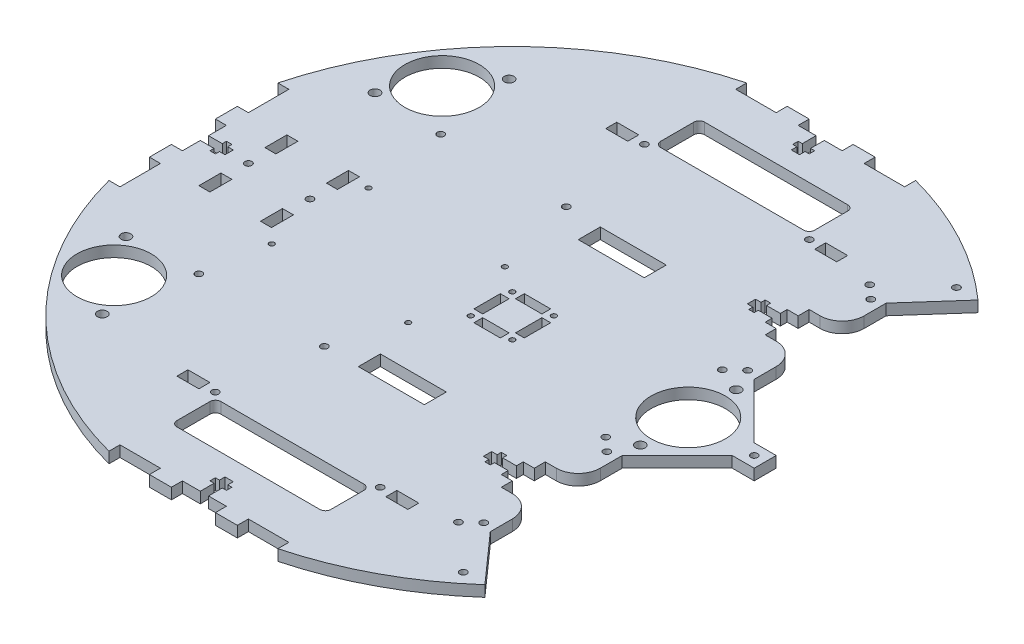
SolidWorks part; units mm, degrees
ref_plane "Front Plane" through (0, 0, 0) normal (0, 0, 1) x (1, 0, 0)
ref_plane "Top Plane" through (0, 0, 0) normal (0, 1, 0) x (1, 0, 0)
ref_plane "Right Plane" through (0, 0, 0) normal (1, 0, 0) x (0, 0, -1)
sketch "Sketch1" plane through (0, 0, 0) normal (0, 1, 0) x (1, 0, 0)
  line L0 (0, 0) -> (0, 177.8)
  line L1 (0, 0) -> (127, 0)
  line L2 (76.2, 82.55) -> (76.2, 69.85)
  line L3 (25.4, 0) -> (25.4, 38.1)
  line L4 (25.4, 38.1) -> (25.4, 114.3)
  line L6 (82.55, -88.9) -> (88.9, -88.9)
  line L7 (101.6, -38.1) -> (127, -12.7)
  line L8 (19.05, -184.15) -> (25.4, -184.15)
  line L9 (101.6, -101.6) -> (101.6, -114.3)
  line L12 (-19.05, -184.15) -> (-25.4, -184.15)
  line L13 (76.2, -82.55) -> (76.2, -69.85)
  line L14 (82.55, 63.5) -> (88.9, 63.5)
  line L15 (101.6, 38.1) -> (101.6, 50.8)
  line L16 (82.55, -63.5) -> (82.55, -69.85)
  line L17 (101.6, -38.1) -> (101.6, -50.8)
  line L18 (88.9, -63.5) -> (82.55, -63.5)
  line L19 (-25.4, -177.8) -> (-25.4, -184.15)
  line L20 (-177.8, -25.4) -> (-184.15, -25.4)
  line L21 (101.6, 38.1) -> (127, 12.7)
  line L22 (82.55, 88.9) -> (88.9, 88.9)
  line L23 (133.35, -6.35) -> (146.05, -6.35)
  line L24 (101.6, 114.3) -> (126.5613, 142.3815)
  line L25 (101.6, -114.3) -> (126.5613, -142.3815)
  line L26 (101.6, 101.6) -> (101.6, 114.3)
  line L27 (0, 0) -> (-177.8, 0)
  line L28 (133.35, 6.35) -> (146.05, 6.35)
  line L29 (146.05, -6.35) -> (146.05, 6.35)
  line L30 (-177.8, 0) -> (-177.8, 6.35)
  line L31 (-177.8, 0) -> (-177.8, -6.35)
  line L32 (-184.15, 48.7753) -> (-177.8, 48.7753)
  line L33 (-19.05, 184.15) -> (-25.4, 184.15)
  line L34 (0, 177.8) -> (6.35, 177.8)
  line L35 (-25.4, 177.8) -> (-25.4, 184.15)
  line L36 (-184.15, 19.05) -> (-184.15, 12.7)
  line L37 (82.55, -69.85) -> (76.2, -69.85)
  line L38 (-177.8, 48.7753) -> (-177.8, 25.4)
  line L39 (76.2, 82.55) -> (82.55, 82.55)
  line L40 (-184.15, -12.7) -> (-184.15, -19.05)
  line L41 (-184.15, -19.05) -> (-184.15, -25.4)
  line L42 (-184.15, -48.7753) -> (-177.8, -48.7753)
  line L43 (-177.8, -48.7753) -> (-177.8, -25.4)
  line L44 (82.55, 88.9) -> (82.55, 82.55)
  line L45 (25.4, -177.8) -> (25.4, -184.15)
  line L46 (0, 177.8) -> (-6.35, 177.8)
  line L47 (48.7753, 184.15) -> (48.7753, 177.8)
  line L48 (19.05, 184.15) -> (25.4, 184.15)
  line L51 (19.05, 184.15) -> (12.7, 184.15)
  line L52 (76.2, 69.85) -> (82.55, 69.85)
  line L53 (48.7753, 177.8) -> (25.4, 177.8)
  line L54 (82.55, 63.5) -> (82.55, 69.85)
  line L55 (-12.7, 184.15) -> (-19.05, 184.15)
  line L56 (-48.7753, 184.15) -> (-48.7753, 177.8)
  line L57 (-48.7753, 177.8) -> (-25.4, 177.8)
  line L58 (127, 12.7) -> (133.35, 6.35)
  line L59 (127, -12.7) -> (133.35, -6.35)
  line L60 (-177.8, -6.35) -> (-177.8, -12.7)
  line L61 (-6.35, -177.8) -> (-12.7, -177.8)
  line L62 (-12.7, -184.15) -> (-12.7, -177.8)
  line L63 (-177.8, -12.7) -> (-184.15, -12.7)
  line L64 (25.4, 177.8) -> (25.4, 184.15)
  line L65 (6.35, -177.8) -> (12.7, -177.8)
  line L66 (12.7, -184.15) -> (12.7, -177.8)
  line L67 (-6.35, 177.8) -> (-12.7, 177.8)
  line L68 (-177.8, 6.35) -> (-177.8, 12.7)
  line L69 (-177.8, 12.7) -> (-184.15, 12.7)
  line L70 (0, -177.8) -> (-6.35, -177.8)
  line L71 (0, -177.8) -> (6.35, -177.8)
  line L72 (-48.7753, -184.15) -> (-48.7753, -177.8)
  line L73 (82.55, -88.9) -> (82.55, -82.55)
  line L74 (82.55, -82.55) -> (76.2, -82.55)
  line L75 (-19.05, -184.15) -> (-12.7, -184.15)
  line L76 (-184.15, 19.05) -> (-184.15, 25.4)
  line L77 (-48.7753, -177.8) -> (-25.4, -177.8)
  line L78 (-184.15, 25.4) -> (-177.8, 25.4)
  line L79 (12.7, -184.15) -> (19.05, -184.15)
  line L80 (48.7753, -184.15) -> (48.7753, -177.8)
  line L81 (48.7753, -177.8) -> (25.4, -177.8)
  line L82 (177.8, 0) -> (177.8, -6.35) [skipped]
  line L83 (177.8, 0) -> (177.8, 6.35) [skipped]
  line L84 (184.15, -48.7753) -> (177.8, -48.7753) [skipped]
  line L87 (184.15, -19.05) -> (184.15, -6.35) [skipped]
  line L89 (177.8, -48.7753) -> (177.8, -19.05) [skipped]
  line L91 (184.15, 6.35) -> (184.15, 19.05) [skipped]
  line L92 (184.15, 48.7753) -> (177.8, 48.7753) [skipped]
  line L93 (177.8, 48.7753) -> (177.8, 19.05) [skipped]
  line L98 (-12.7, 177.8) -> (-12.7, 184.15)
  line L99 (6.35, 177.8) -> (12.7, 177.8)
  line L102 (12.7, 177.8) -> (12.7, 184.15)
  arc A0 (126.5613, 142.3815) -> (48.7753, 184.15) centre (0, 0) ccw
  arc A1 (-184.15, -48.7753) -> (-48.7753, -184.15) centre (0, 0) ccw
  arc A2 (-48.7753, 184.15) -> (-184.15, 48.7753) centre (0, 0) ccw
  arc A3 (48.7753, -184.15) -> (126.5613, -142.3815) centre (0, 0) ccw
  arc A4 (101.6, 50.8) -> (88.9, 63.5) centre (88.9, 50.8) ccw
  arc A5 (88.9, -63.5) -> (101.6, -50.8) centre (88.9, -50.8) ccw
  arc A6 (101.6, 101.6) -> (88.9, 88.9) centre (88.9, 101.6) cw
  arc A7 (101.6, -101.6) -> (88.9, -88.9) centre (88.9, -101.6) ccw
  point P37 (101.6, 63.5)
  point P67 (101.6, -63.5)
  point P91 (0, 0)
  dimension "D1" = 381
  dimension "D24" = 12.7
  dimension "D25" = 12.7
  dimension "D10" = 12.7
  dimension "D6" = 12.7
  dimension "D2" = 25.4
  dimension "D3" = 38.1
  dimension "D4" = 76.2
  dimension "D5" = 6.35
  dimension "D7" = 6.35
  dimension "D8" = 25.4
  dimension "D9" = 25.4
  dimension "D11" = 12.7
  dimension "D12" = 25.4
  dimension "D13" = 12.7
  dimension "D14" = 12.7
  dimension "D15" = 6.35
  dimension "D16" = 177.8
  dimension "D17" = 6.35
  dimension "D18" = 6.35
  dimension "D19" = 6.35
  dimension "D20" = 6.35
  dimension "D21" = 6.35
  dimension "D22" = 6.35
  dimension "D23" = 4
  dimension "D26" = 6.35
  dimension "D27" = 6.35
  dimension "D28" = 6.35
  dimension "D29" = 6.35
extrude "Boss-Extrude2" add sketch "Sketch1" along normal blind 6.35 contours L31 L60 L63 L40 L41 L20 L43 L42 A1 L72 L77 L19 L12 L75 L62 L61 L70 L71 L65 L66 L79 L8 L45 L81 L80 A3 L25 L9 A7 L6 L73 L74 L13 L37 L16 L18 A5 L17 L7 L59 L23 L29 L28 L58 L21 L15 A4 L14 L54 L52 L2 L39 L44 L22 A6 L26 L24 A0 L47 L53 L64 L48 L51 L102 L99 L34 L46 L67 L98 L55 L33 L35 L57 L56 A2 L32 L38 L78 L76 L36 L69 L68 L30
sketch "Sketch18" plane through (0, 6.35, 0) normal (0, 1, 0) x (1, 0, 0)
  line L0 (0, 0) -> (0, 127)
  line L2 (-41.275, 152.4) -> (41.275, 152.4)
  line L3 (0, 152.4) -> (0, 127)
  line L4 (-41.275, 127) -> (41.275, 127)
  line L5 (44.45, 149.225) -> (44.45, 130.175)
  line L6 (-53.975, 127) -> (-53.975, 120.65)
  line L7 (66.675, 127) -> (53.975, 127)
  line L8 (66.675, 127) -> (66.675, 120.65)
  line L9 (66.675, 120.65) -> (53.975, 120.65)
  line L10 (53.975, 127) -> (53.975, 120.65)
  line L11 (-66.675, 120.65) -> (-53.975, 120.65)
  line L12 (-66.675, 127) -> (-66.675, 120.65)
  line L13 (-66.675, 127) -> (-53.975, 127)
  line L14 (-44.45, 149.225) -> (-44.45, 130.175)
  circle A0 centre (47.625, 123.9148) radius 2
  arc A1 (44.45, 130.175) -> (41.275, 127) centre (41.275, 130.175) cw
  arc A2 (44.45, 149.225) -> (41.275, 152.4) centre (41.275, 149.225) ccw
  arc A3 (-44.45, 149.225) -> (-41.275, 152.4) centre (-41.275, 149.225) cw
  arc A4 (-44.45, 130.175) -> (-41.275, 127) centre (-41.275, 130.175) ccw
  circle A5 centre (-47.625, 123.9148) radius 2
  point P18 (44.45, 152.4)
  point P31 (-44.45, 152.4)
  dimension "D7" = 4
  dimension "D9" = 3.175
  dimension "D1" = 127
  dimension "D2" = 25.4
  dimension "D3" = 44.45
  dimension "D4" = 12.7
  dimension "D5" = 6.35
  dimension "D6" = 53.975
  dimension "D8" = 6.35
extrude "Cut-Extrude15" cut sketch "Sketch18" against normal blind 6.35
mirror "Mirror5" about plane through (0, 0, 0) normal (0, 0, 1) of "Cut-Extrude15"
sketch "Sketch19" plane through (0, 6.35, 0) normal (0, 1, 0) x (1, 0, 0)
  line L0 (0, 0) -> (101.6, 0)
  line L1 (101.6, 0) -> (101.6, 66.0006)
  circle A0 centre (101.6, 0) radius 21.463
  circle A1 centre (101.6, 27.686) radius 2.794
  circle A2 centre (101.6, -27.686) radius 2.794
  dimension "D1" = 42.926
  dimension "D2" = 5.588
  dimension "D3" = 27.686
  dimension "D4" = 101.6
extrude "Cut-Extrude16" cut sketch "Sketch19" against normal blind 6.35 contours L1 A0 L0 | L0 A0 L1 | A2 | A1
sketch "Sketch20" plane through (0, 6.35, 0) normal (0, 1, 0) x (1, 0, 0)
  line L0 (0, 0) -> (-161.6538, 0)
  line L1 (-161.6538, 0) -> (0, 0)
  line L2 (0, 0) -> (-135.242, 94.6975)
  line L3 (-135.242, 94.6975) -> (-83.5434, 168.5307)
  circle A0 centre (-135.242, 94.6975) radius 21.463
  circle A1 centre (-119.2891, 117.4805) radius 2.794
  circle A2 centre (-151.1949, 71.9144) radius 2.794
  circle A3 centre (-151.1949, -71.9144) radius 2.794
  circle A4 centre (-119.2891, -117.4805) radius 2.794
  circle A5 centre (-135.242, -94.6975) radius 21.463
  dimension "D2" = 42.926
  dimension "D3" = 5.588
  dimension "D1" = 35
  dimension "D4" = 27.813
  dimension "D5" = 165.1
extrude "Cut-Extrude17" cut sketch "Sketch20" against normal blind 6.35 contours L2 A0 L3 | L3 A0 L2 | L3 A1 | L3 A1 | A2 | A5 | A4 | A3
sketch "Sketch21" plane through (0, 6.35, 0) normal (0, 1, 0) x (1, 0, 0)
  line L0 (0, 0) -> (-152.4, 0)
  line L1 (-152.4, 0) -> (-152.4, 25.4)
  line L2 (-149.225, 25.4) -> (-149.225, 12.7)
  line L3 (-155.575, 25.4) -> (-149.225, 25.4)
  line L4 (-155.575, 25.4) -> (-155.575, 12.7)
  line L5 (-155.575, 12.7) -> (-149.225, 12.7)
  line L6 (-152.4, 25.4) -> (-152.4, 12.7)
  line L7 (-152.4, -25.4) -> (-152.4, -12.7)
  line L8 (-155.575, -12.7) -> (-149.225, -12.7)
  line L9 (-155.575, -25.4) -> (-155.575, -12.7)
  line L10 (-155.575, -25.4) -> (-149.225, -25.4)
  line L11 (-149.225, -25.4) -> (-149.225, -12.7)
  circle A0 centre (-152.4, 0) radius 2
  dimension "D5" = 4
  dimension "D1" = 152.4
  dimension "D2" = 12.7
  dimension "D3" = 12.7
  dimension "D4" = 3.175
extrude "Cut-Extrude18" cut sketch "Sketch21" against normal blind 6.35 contours L1 L5 L2 L3 | L4 L5 L1 L3 | A0 | L11 L8 L9 L10
sketch "Sketch23" plane through (0, 6.35, 0) normal (0, 1, 0) x (1, 0, 0)
  line L2 (-120.015, 12.7) -> (-120.015, 25.4)
  line L3 (-113.665, 12.7) -> (-120.015, 12.7)
  line L4 (-113.665, 12.7) -> (-113.665, 25.4)
  line L5 (-113.665, 25.4) -> (-120.015, 25.4)
  line L8 (-113.665, -25.4) -> (-120.015, -25.4)
  line L9 (-113.665, -12.7) -> (-113.665, -25.4)
  line L10 (-113.665, -12.7) -> (-120.015, -12.7)
  line L11 (-120.015, -12.7) -> (-120.015, -25.4)
  circle A1 centre (-116.84, 0) radius 2
  dimension "D1" = 4
  dimension "D6" = 0
  dimension "D2" = 6.35
  dimension "D3" = 12.7
  dimension "D4" = 25.4
  dimension "D5" = 12.7
  dimension "D7" = 116.84
extrude "Cut-Extrude27" cut sketch "Sketch23" against normal blind 6.35
sketch "Sketch27" plane through (0, 6.35, 0) normal (0, 1, 0) x (1, 0, 0)
  line L2 (76.2, 73.8188) -> (76.2, 78.5813)
  line L3 (76.2, 78.5813) -> (68.2625, 78.5813)
  line L4 (76.2, -73.8188) -> (68.2625, -73.8188)
  line L5 (65.0875, 71.4375) -> (65.0875, 73.8188)
  line L6 (65.0875, -73.8188) -> (61.9125, -73.8188)
  line L7 (68.2625, -71.4375) -> (65.0875, -71.4375)
  line L8 (68.2625, -71.4375) -> (68.2625, -73.8188)
  line L9 (65.0875, -80.9625) -> (65.0875, -78.5813)
  line L10 (65.0875, 78.5813) -> (61.9125, 78.5813)
  line L11 (68.2625, -80.9625) -> (68.2625, -78.5813)
  line L12 (68.2625, -80.9625) -> (65.0875, -80.9625)
  line L13 (61.9125, 78.5813) -> (61.9125, 73.8188)
  line L14 (68.2625, 80.9625) -> (65.0875, 80.9625)
  line L15 (68.2625, 80.9625) -> (68.2625, 78.5813)
  line L16 (61.9125, -78.5813) -> (61.9125, -73.8188)
  line L17 (65.0875, 80.9625) -> (65.0875, 78.5813)
  line L18 (65.0875, -78.5813) -> (61.9125, -78.5813)
  line L19 (68.2625, 71.4375) -> (68.2625, 73.8188)
  line L20 (68.2625, 71.4375) -> (65.0875, 71.4375)
  line L21 (65.0875, 73.8188) -> (61.9125, 73.8188)
  line L22 (65.0875, -71.4375) -> (65.0875, -73.8188)
  line L23 (76.2, 73.8188) -> (68.2625, 73.8188)
  line L24 (76.2, -78.5813) -> (68.2625, -78.5813)
  line L25 (76.2, -73.8188) -> (76.2, -78.5813)
  dimension "D2" = 2.3813
sketch "Sketch32" plane through (0, 6.35, 0) normal (0, 1, 0) x (1, 0, 0)
  line L0 (14.5415, -7.62) -> (14.5415, 7.62)
  line L1 (-12.0015, -12.0015) -> (12.0015, -12.0015) construction
  line L2 (-12.0015, -12.0015) -> (-12.0015, 12.0015) construction
  line L3 (-12.0015, 12.0015) -> (12.0015, 12.0015) construction
  line L4 (12.0015, -12.0015) -> (12.0015, 12.0015) construction
  line L5 (-12.0015, -12.0015) -> (12.0015, 12.0015) construction
  line L6 (-12.0015, 12.0015) -> (12.0015, -12.0015) construction
  line L7 (7.62, 14.5415) -> (-7.62, 14.5415)
  line L8 (7.62, 14.5415) -> (7.62, 9.4615)
  line L9 (7.62, 9.4615) -> (-7.62, 9.4615)
  line L10 (-7.62, 14.5415) -> (-7.62, 9.4615)
  line L11 (7.62, 14.5415) -> (-7.62, 9.4615) construction
  line L12 (7.62, 9.4615) -> (-7.62, 14.5415) construction
  line L13 (14.5415, -7.62) -> (9.4615, -7.62)
  line L14 (9.4615, -7.62) -> (9.4615, 7.62)
  line L15 (14.5415, 7.62) -> (9.4615, 7.62)
  line L16 (12.0015, 12.0015) -> (12.0015, -12.0015) construction
  line L17 (14.5415, -7.62) -> (9.4615, 7.62) construction
  line L18 (9.4615, -7.62) -> (14.5415, 7.62) construction
  line L19 (-7.62, -14.5415) -> (7.62, -14.5415)
  line L20 (-7.62, -14.5415) -> (-7.62, -9.4615)
  line L21 (-7.62, -9.4615) -> (7.62, -9.4615)
  line L22 (7.62, -14.5415) -> (7.62, -9.4615)
  line L23 (12.0015, -12.0015) -> (-12.0015, -12.0015) construction
  line L24 (-7.62, -14.5415) -> (7.62, -9.4615) construction
  line L25 (-7.62, -9.4615) -> (7.62, -14.5415) construction
  line L26 (-14.5415, 7.62) -> (-14.5415, -7.62)
  line L27 (-14.5415, 7.62) -> (-9.4615, 7.62)
  line L28 (-9.4615, 7.62) -> (-9.4615, -7.62)
  line L29 (-14.5415, -7.62) -> (-9.4615, -7.62)
  line L31 (-12.0015, -12.0015) -> (-12.0015, 12.0015) construction
  line L32 (-14.5415, 7.62) -> (-9.4615, -7.62) construction
  line L33 (-9.4615, 7.62) -> (-14.5415, -7.62) construction
  circle A0 centre (12.0015, 12.0015) radius 1.5
  circle A1 centre (12.0015, -12.0015) radius 1.5
  circle A2 centre (-12.0015, -12.0015) radius 1.5
  circle A3 centre (-12.0015, 12.0015) radius 1.5
  point P0 (0, 0)
  point P6 (0, 12.0015)
  point P17 (12.0015, 0)
  point P25 (0, -12.0015)
  point P33 (-12.0015, 0)
  point P45 (0, 0)
  dimension "D3" = 15.24
  dimension "D5" = 3
  dimension "D1" = 24.003
  dimension "D2" = 24.003
  dimension "D4" = 5.08
extrude "Cut-Extrude32" cut sketch "Sketch32" against normal blind 6.35
sketch "Sketch33" plane through (0, 6.35, 0) normal (0, 1, 0) x (1, 0, 0)
  line L0 (0, 0) -> (0, 127)
  line L1 (-41.275, 127) -> (41.275, 127) construction
  line L2 (0, 0) -> (25.4678, 0)
  line L3 (19.05, 69.85) -> (-19.05, 69.85)
  line L4 (19.05, 69.85) -> (19.05, 57.15)
  line L5 (19.05, 57.15) -> (-19.05, 57.15)
  line L6 (-19.05, 69.85) -> (-19.05, 57.15)
  line L7 (19.05, 69.85) -> (-19.05, 57.15) construction
  line L8 (19.05, 57.15) -> (-19.05, 69.85) construction
  line L9 (19.05, -57.15) -> (-19.05, -69.85) construction
  line L10 (19.05, -69.85) -> (-19.05, -57.15) construction
  line L11 (-19.05, -69.85) -> (-19.05, -57.15)
  line L12 (19.05, -57.15) -> (-19.05, -57.15)
  line L13 (19.05, -69.85) -> (19.05, -57.15)
  line L14 (19.05, -69.85) -> (-19.05, -69.85)
  point P5 (0, 63.5)
  point P15 (0, -63.5)
  dimension "D1" = 57.15
  dimension "D2" = 12.7
  dimension "D3" = 38.1
extrude "Cut-Extrude33" cut sketch "Sketch33" against normal blind 6.35 contours L3 L6 L5 L4 | L12 L11 L14 L13
sketch "Sketch37" plane through (0, 6.35, 0) normal (0, 1, 0) x (1, 0, 0)
  line L1 (-105.4183, -33.4858) -> (-26.6783, -33.4858)
  line L2 (-105.4183, -33.4858) -> (-105.4183, 22.3942)
  line L3 (-105.4183, 22.3942) -> (-26.6783, 22.3942)
  line L4 (-26.6783, -33.4858) -> (-26.6783, 22.3942)
  line L5 (-105.4183, -33.4858) -> (-26.6783, 22.3942) construction
  line L6 (-105.4183, 22.3942) -> (-26.6783, -33.4858) construction
  circle A0 centre (-105.4183, 22.3942) radius 1.5
  circle A1 centre (-26.6783, 22.3942) radius 1.5
  circle A2 centre (-26.6783, -33.4858) radius 1.5
  circle A3 centre (-105.4183, -33.4858) radius 1.5
  point P0 (-66.0483, -5.5458)
  dimension "D3" = 3
  dimension "D1" = 78.74
  dimension "D2" = 55.88
  dimension "D4" = 2
  dimension "D5" = 2
extrude "Cut-Extrude37" cut sketch "Sketch37" against normal blind 6.35 contours A0 | A1 | A2 | A3
sketch "Sketch38" plane through (0, 6.35, 0) normal (0, 1, 0) x (1, 0, 0)
  line L1 (-39.0054, 70.157) -> (-111.5054, 70.157)
  line L2 (-39.0054, 70.157) -> (-39.0054, -69.543)
  line L3 (-39.0054, -69.543) -> (-111.5054, -69.543)
  line L4 (-111.5054, 70.157) -> (-111.5054, -69.543)
  line L5 (-39.0054, 70.157) -> (-111.5054, -69.543) construction
  line L6 (-39.0054, -69.543) -> (-111.5054, 70.157) construction
  circle A0 centre (-39.0054, 70.157) radius 2
  circle A1 centre (-111.5054, 70.157) radius 2
  circle A2 centre (-111.5054, -69.543) radius 2
  circle A3 centre (-39.0054, -69.543) radius 2
  point P0 (-75.2554, 0.307)
  dimension "D3" = 4
  dimension "D1" = 72.5
  dimension "D2" = 139.7
  dimension "D4" = 2
  dimension "D5" = 2
extrude "Cut-Extrude38" cut sketch "Sketch38" against normal blind 6.35 contours A1 | A0 | A3 | A2
extrude "Cut-Extrude30" cut sketch "Sketch27" against normal blind 6.35
sketch "Sketch29" plane through (0, 6.35, 0) normal (0, 1, 0) x (1, 0, 0)
  line L0 (-2.3812, 177.8) -> (2.3813, 177.8)
  line L1 (2.3813, 177.8) -> (2.3813, 169.8625)
  line L2 (-177.8, -2.3813) -> (-177.8, 2.3812)
  line L3 (-177.8, 2.3812) -> (-169.8625, 2.3812)
  line L4 (2.3813, 169.8625) -> (4.7625, 169.8625)
  line L5 (4.7625, 169.8625) -> (4.7625, 166.6875)
  line L6 (2.3813, 166.6875) -> (4.7625, 166.6875)
  line L7 (2.3813, 166.6875) -> (2.3813, 163.5125)
  line L8 (2.3813, 163.5125) -> (-2.3812, 163.5125)
  line L9 (-2.3812, 166.6875) -> (-2.3812, 163.5125)
  line L10 (-169.8625, 2.3812) -> (-169.8625, 4.7625)
  line L11 (-169.8625, 4.7625) -> (-166.6875, 4.7625)
  line L12 (-166.6875, 2.3812) -> (-166.6875, 4.7625)
  line L13 (-166.6875, 2.3812) -> (-163.5125, 2.3812)
  line L14 (-2.3812, 166.6875) -> (-4.7625, 166.6875)
  line L15 (-4.7625, 169.8625) -> (-4.7625, 166.6875)
  line L16 (-163.5125, 2.3812) -> (-163.5125, -2.3813)
  line L17 (-166.6875, -2.3813) -> (-163.5125, -2.3813)
  line L18 (-166.6875, -2.3813) -> (-166.6875, -4.7625)
  line L19 (-169.8625, -4.7625) -> (-166.6875, -4.7625)
  line L20 (-169.8625, -2.3813) -> (-169.8625, -4.7625)
  line L21 (-2.3812, 169.8625) -> (-4.7625, 169.8625)
  line L22 (-2.3812, 177.8) -> (-2.3812, 169.8625)
  line L23 (-177.8, -2.3813) -> (-169.8625, -2.3813)
  line L36 (2.3812, -177.8) -> (-2.3813, -177.8)
  line L37 (-2.3813, -177.8) -> (-2.3813, -169.8625)
  line L38 (-2.3813, -169.8625) -> (-4.7625, -169.8625)
  line L39 (-4.7625, -169.8625) -> (-4.7625, -166.6875)
  line L40 (-2.3813, -166.6875) -> (-4.7625, -166.6875)
  line L41 (-2.3813, -166.6875) -> (-2.3813, -163.5125)
  line L42 (-2.3813, -163.5125) -> (2.3812, -163.5125)
  line L43 (2.3812, -166.6875) -> (2.3812, -163.5125)
  line L44 (2.3812, -166.6875) -> (4.7625, -166.6875)
  line L45 (4.7625, -169.8625) -> (4.7625, -166.6875)
  line L46 (2.3812, -169.8625) -> (4.7625, -169.8625)
  line L47 (2.3812, -177.8) -> (2.3812, -169.8625)
  line L48 (177.8, 2.3812) -> (177.8, -2.3813) [skipped]
  line L49 (177.8, -2.3813) -> (169.8625, -2.3813) [skipped]
  line L50 (169.8625, -2.3813) -> (169.8625, -4.7625) [skipped]
  line L51 (169.8625, -4.7625) -> (166.6875, -4.7625) [skipped]
  line L52 (166.6875, -2.3813) -> (166.6875, -4.7625) [skipped]
  line L53 (166.6875, -2.3813) -> (163.5125, -2.3813) [skipped]
  line L54 (163.5125, -2.3813) -> (163.5125, 2.3812) [skipped]
  line L55 (166.6875, 2.3812) -> (163.5125, 2.3812) [skipped]
  line L56 (166.6875, 2.3812) -> (166.6875, 4.7625) [skipped]
  line L57 (169.8625, 4.7625) -> (166.6875, 4.7625) [skipped]
  line L58 (169.8625, 2.3812) -> (169.8625, 4.7625) [skipped]
  line L59 (177.8, 2.3812) -> (169.8625, 2.3812) [skipped]
  point P51 (0, 0)
  dimension "D1" = 4
  dimension "D3" = 2.3813
  dimension "D4" = 3.175
  dimension "D5" = 7.9375
  dimension "D6" = 3.175
extrude "Cut-Extrude31" cut sketch "Sketch29" against normal blind 6.35
sketch "Sketch39" plane through (0, 6.35, 0) normal (0, 1, 0) x (1, 0, 0)
  line L0 (101.6, 38.1) -> (76.4458, 12.9458)
  line L1 (82.55, 63.5) -> (101.6, 63.5)
  line L3 (82.55, 38.1) -> (101.6, 38.1)
  line L4 (101.6, 63.5) -> (101.6, 38.1)
  line L5 (92.075, 38.1) -> (73.025, 38.1)
  line L6 (82.55, 38.1) -> (82.55, 63.5)
  line L7 (82.55, 63.5) -> (82.55, 38.1)
  line L8 (82.55, 19.05) -> (82.55, 38.1)
  line L9 (92.075, 28.575) -> (82.55, 28.575)
  line L10 (101.6, 38.1) -> (101.6, 50.8)
  line L11 (0, 0) -> (55.663, 0)
  line L12 (101.6, -114.3) -> (101.6, -101.6)
  line L13 (92.075, -123.825) -> (82.55, -123.825)
  line L14 (82.55, -133.35) -> (82.55, -114.3)
  line L15 (101.6, -114.3) -> (82.55, -133.35)
  line L16 (82.55, -114.3) -> (101.6, -114.3)
  line L17 (101.6, -88.9) -> (101.6, -114.3)
  line L18 (76.2, -114.3) -> (101.6, -114.3)
  line L19 (76.2, -88.9) -> (76.2, -114.3)
  line L20 (76.2, -88.9) -> (101.6, -88.9)
  line L21 (82.55, -88.9) -> (82.55, -114.3)
  line L22 (101.6, -38.1) -> (101.6, -50.8)
  line L23 (82.55, 88.9) -> (82.55, 114.3)
  line L24 (82.55, 88.9) -> (101.6, 88.9)
  line L26 (82.55, 114.3) -> (101.6, 114.3)
  line L27 (101.6, 88.9) -> (101.6, 114.3)
  line L28 (82.55, 114.3) -> (101.6, 114.3)
  line L29 (101.6, 114.3) -> (82.55, 133.35)
  line L30 (82.55, 133.35) -> (82.55, 114.3)
  line L31 (92.075, 123.825) -> (82.55, 123.825)
  line L32 (101.6, 114.3) -> (101.6, 101.6)
  line L33 (92.075, -28.575) -> (82.55, -28.575)
  line L34 (82.55, -19.05) -> (82.55, -38.1)
  line L35 (82.55, -63.5) -> (82.55, -38.1)
  line L36 (82.55, -38.1) -> (82.55, -63.5)
  line L37 (92.075, -38.1) -> (82.55, -38.1)
  line L38 (101.6, -63.5) -> (101.6, -38.1)
  line L39 (82.55, -38.1) -> (101.6, -38.1)
  line L41 (82.55, -63.5) -> (101.6, -63.5)
  line L42 (101.6, -38.1) -> (76.4458, -12.9458)
  circle A0 centre (87.63, 33.655) radius 2
  circle A1 centre (95.25, 40.64) radius 2
  circle A3 centre (95.25, -111.76) radius 2
  circle A4 centre (87.63, -118.745) radius 2
  circle A5 centre (87.63, 118.745) radius 2
  circle A6 centre (95.25, 111.76) radius 2
  circle A7 centre (95.25, -40.64) radius 2
  circle A8 centre (87.63, -33.655) radius 2
  dimension "D1" = 4
  dimension "D2" = 4
  dimension "D5" = 10.16
  dimension "D7" = 4
  dimension "D8" = 4
  dimension "D9" = 5.08
  dimension "D11" = 10.16
  dimension "D12" = 6.35
  dimension "D3" = 5.08
  dimension "D4" = 5.08
  dimension "D6" = 6.35
  dimension "D10" = 5.08
  dimension "D13" = 19.05
extrude "Cut-Extrude41" cut sketch "Sketch39" against normal blind 6.35 contours A0 | A3 | A4 | A7 | A8 | A1 | A6 | A5
sketch "Sketch40" plane through (0, 6.35, 0) normal (0, 1, 0) x (1, 0, 0)
  circle A0 centre (139.7, 0) radius 2
  dimension "D1" = 4
extrude "Cut-Extrude42" cut sketch "Sketch40" against normal blind 6.35
sketch "Sketch41" plane through (0, 6.35, 0) normal (0, 1, 0) x (1, 0, 0)
  line L0 (0, 0) -> (126.5613, 142.3815)
  line L1 (101.6, 114.3) -> (101.6, 142.3815)
  line L2 (101.6, 101.6) -> (101.6, 114.3) construction
  line L3 (126.5613, 142.3815) -> (101.6, 142.3815)
  line L4 (0, 0) -> (23.9176, 0)
  circle A0 centre (114.0807, 142.3815) radius 2
  circle A1 centre (114.0807, -142.3815) radius 2
  dimension "D1" = 4
extrude "Cut-Extrude43" cut sketch "Sketch41" against normal blind 6.35 contours A0 | A1
